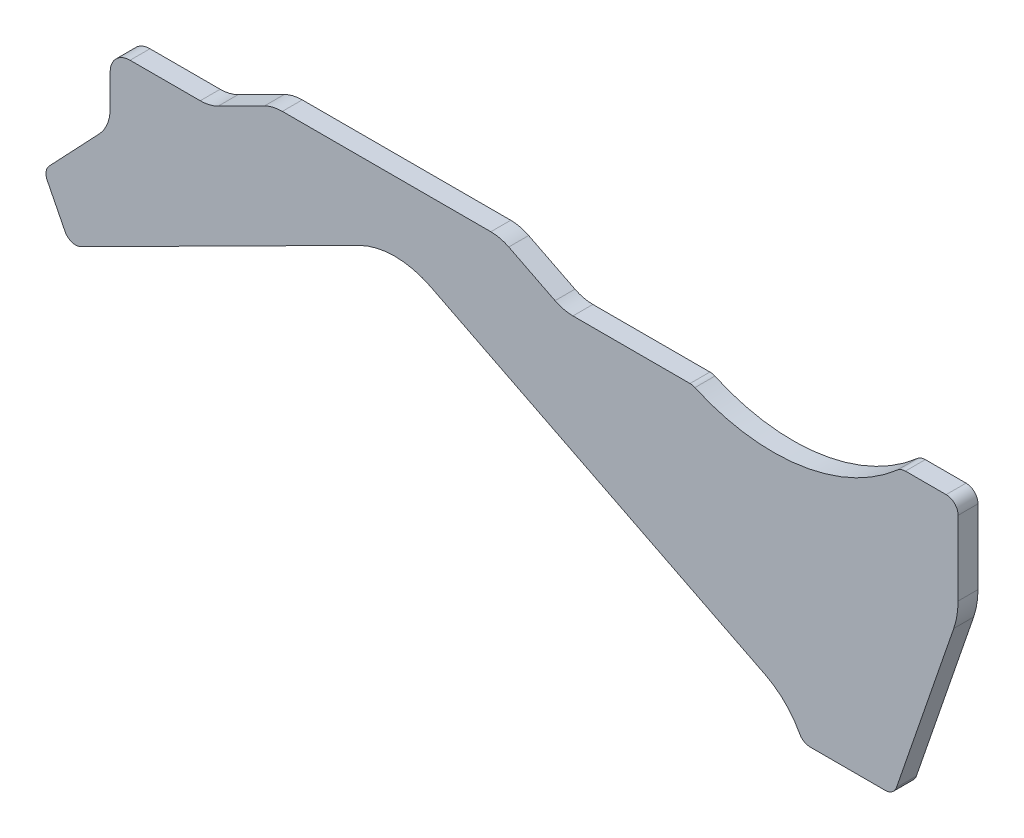
SolidWorks part; units mm, degrees
ref_plane "Plane1" through (0, 0, 0) normal (0, 0, 1) x (1, 0, 0)
ref_plane "Plane2" through (0, 0, 0) normal (0, 1, 0) x (1, 0, 0)
ref_plane "Plane3" through (0, 0, 0) normal (1, 0, 0) x (0, 0, -1)
sketch "Sketch1" plane through (0, 0, 0) normal (0, 0, 1) x (1, 0, 0)
  line L0 (9.002, -4.5374) -> (93.002, -46.8769)
  line L1 (126.0133, -54.9767) -> (140.4104, -13.1645)
  line L2 (141.5, -6.6531) -> (141.5, 12)
  line L3 (138.5, 15) -> (128.2603, 15)
  line L5 (0, 0) -> (0, -41.1004) construction
  line L6 (-9.002, -4.5374) -> (-78.8211, -39.7291)
  line L7 (-28.2506, 15) -> (24.1223, 15)
  line L8 (123.1767, -57) -> (104.3403, -57)
  line L9 (-32.7515, 13.9298) -> (-44.3767, 8.0702)
  line L10 (-48.8777, 7) -> (-66.5, 7)
  line L11 (44.7494, 7) -> (74.1613, 7)
  line L12 (-71.5, 2) -> (-71.5, -6.0157)
  line L13 (-87.3025, -29.5674) -> (-82.8503, -38.4004)
  line L14 (40.2485, 8.0702) -> (28.6233, 13.9298)
  line L19 (-74.24, -12.8926) -> (-86.8016, -26.154)
  arc A0 (9.002, -4.5374) -> (-9.002, -4.5374) centre (0, -22.3969) ccw
  arc A1 (-78.8211, -39.7291) -> (-82.8503, -38.4004) centre (-80.1714, -37.0501) cw
  arc A2 (-86.8016, -26.154) -> (-87.3025, -29.5674) centre (-84.6236, -28.2171) ccw
  arc A3 (-66.5, 7) -> (-71.5, 2) centre (-66.5, 2) ccw
  arc A4 (75.3993, 6.7327) -> (126.2845, 14.2574) centre (95, 50) ccw
  arc A5 (128.2603, 15) -> (126.2845, 14.2574) centre (128.2603, 12) ccw
  arc A6 (141.5, 12) -> (138.5, 15) centre (138.5, 12) ccw
  arc A7 (75.3993, 6.7327) -> (74.1613, 7) centre (74.1613, 4) ccw
  arc A8 (101.6872, -55.4004) -> (93.002, -46.8769) centre (84, -64.7364) ccw
  arc A9 (123.1767, -57) -> (126.0133, -54.9767) centre (123.1767, -54) ccw
  arc A10 (104.3403, -57) -> (101.6872, -55.4004) centre (104.3403, -54) cw
  arc A11 (-44.3767, 8.0702) -> (-48.8777, 7) centre (-48.8777, 17) cw
  arc A12 (-32.7515, 13.9298) -> (-28.2506, 15) centre (-28.2506, 5) cw
  arc A13 (44.7494, 7) -> (40.2485, 8.0702) centre (44.7494, 17) cw
  arc A14 (28.6233, 13.9298) -> (24.1223, 15) centre (24.1223, 5) ccw
  arc A15 (140.4104, -13.1645) -> (141.5, -6.6531) centre (121.5, -6.6531) ccw
  arc A16 (-71.5, -6.0157) -> (-74.24, -12.8926) centre (-81.5, -6.0157) cw
  point P14 (-81.5, -41.0794)
  point P17 (127.1131, 15)
  point P18 (26.5, 15)
  point P23 (-88.2515, -27.6847)
  point P26 (-71.5, 7)
  point P44 (-46.5, 7)
  point P51 (42.3717, 7)
  point P56 (141.5, -10)
  point P59 (-71.5, -10)
  dimension "D15" = 20
  dimension "D11" = 8
  dimension "D10" = 10
  dimension "D13" = 35
  dimension "D19" = 20
  dimension "D20" = 3
  dimension "D21" = 3
  dimension "D16" = 3
  dimension "D22" = 5
  dimension "D25" = 47.5
  dimension "D26" = 20
  dimension "D27" = 10
  dimension "D29" = 10
  dimension "D9" = 3
  dimension "D1" = 63.25
  dimension "D2" = 63.25
  dimension "D3" = 115
  dimension "D4" = 81.5
  dimension "D5" = 15
  dimension "D6" = 141.5
  dimension "D7" = 19
  dimension "D8" = 25
  dimension "D12" = 84
  dimension "D14" = 71.5
  dimension "D17" = 72
  dimension "D18" = 25
  dimension "D23" = 15
  dimension "D24" = 46.5
  dimension "D28" = 17
extrude "Extrude1" add sketch "Sketch1" along normal blind 5
